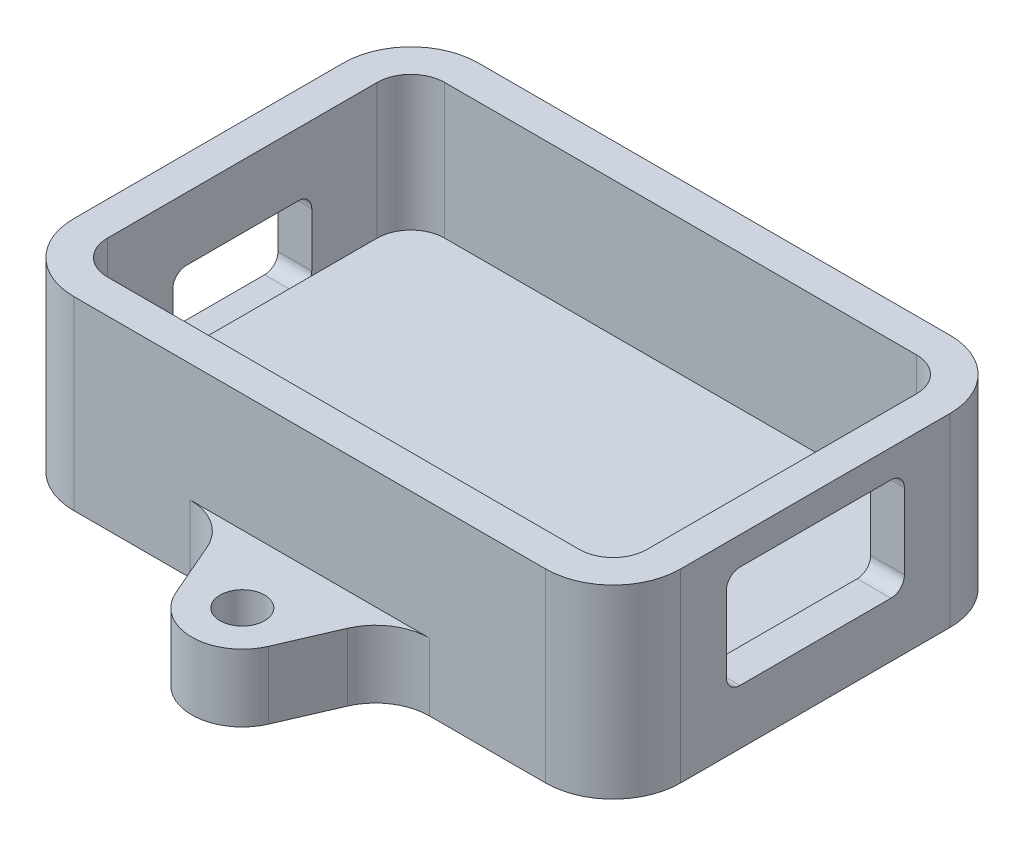
SolidWorks part; units mm, degrees
material "PVC Rigid"
ref_plane "Front Plane" through (0, 0, 0) normal (0, 0, 1) x (1, 0, 0)
ref_plane "Top Plane" through (0, 0, 0) normal (0, 1, 0) x (1, 0, 0)
ref_plane "Right Plane" through (0, 0, 0) normal (1, 0, 0) x (0, 0, -1)
sketch "Sketch1" plane through (0, 0, 0) normal (0, 1, 0) x (1, 0, 0)
  line L1 (-22.225, -19.05) -> (22.225, -19.05)
  line L2 (-28.575, -12.7) -> (-28.575, 12.7)
  line L3 (-22.225, 19.05) -> (22.225, 19.05)
  line L4 (28.575, -12.7) -> (28.575, 12.7)
  line L5 (-28.575, -19.05) -> (28.575, 19.05) construction
  line L6 (-28.575, 19.05) -> (28.575, -19.05) construction
  arc A0 (-22.225, -19.05) -> (-28.575, -12.7) centre (-22.225, -12.7) cw
  arc A1 (22.225, -19.05) -> (28.575, -12.7) centre (22.225, -12.7) ccw
  arc A2 (22.225, 19.05) -> (28.575, 12.7) centre (22.225, 12.7) cw
  arc A3 (-28.575, 12.7) -> (-22.225, 19.05) centre (-22.225, 12.7) cw
  point P0 (0, 0)
  dimension "D3" = 6.35
  dimension "D1" = 57.15
  dimension "D2" = 38.1
extrude "Boss-Extrude1" add sketch "Sketch1" along normal blind 4.7625
sketch "Sketch2" plane through (0, 4.7625, 0) normal (0, 1, 0) x (1, 0, 0)
  line L1 (-22.225, -15.875) -> (22.225, -15.875)
  line L2 (25.4, -12.7) -> (25.4, 12.7)
  line L3 (22.225, 15.875) -> (-22.225, 15.875)
  line L4 (-25.4, 12.7) -> (-25.4, -12.7)
  line L5 (-22.225, -19.05) -> (22.225, -19.05)
  line L6 (28.575, -12.7) -> (28.575, 12.7)
  line L7 (22.225, 19.05) -> (-22.225, 19.05)
  line L8 (-28.575, 12.7) -> (-28.575, -12.7)
  line L9 (-22.225, -19.05) -> (22.225, -19.05)
  line L10 (28.575, -12.7) -> (28.575, 12.7)
  line L11 (22.225, 19.05) -> (-22.225, 19.05)
  line L12 (-28.575, 12.7) -> (-28.575, -12.7)
  arc A0 (-25.4, -12.7) -> (-22.225, -15.875) centre (-22.225, -12.7) ccw
  arc A1 (22.225, -15.875) -> (25.4, -12.7) centre (22.225, -12.7) ccw
  arc A2 (25.4, 12.7) -> (22.225, 15.875) centre (22.225, 12.7) ccw
  arc A3 (-22.225, 15.875) -> (-25.4, 12.7) centre (-22.225, 12.7) ccw
  arc A4 (-28.575, -12.7) -> (-22.225, -19.05) centre (-22.225, -12.7) ccw
  arc A5 (22.225, -19.05) -> (28.575, -12.7) centre (22.225, -12.7) ccw
  arc A6 (28.575, 12.7) -> (22.225, 19.05) centre (22.225, 12.7) ccw
  arc A7 (-22.225, 19.05) -> (-28.575, 12.7) centre (-22.225, 12.7) ccw
  arc A8 (-28.575, -12.7) -> (-22.225, -19.05) centre (-22.225, -12.7) ccw
  arc A9 (22.225, -19.05) -> (28.575, -12.7) centre (22.225, -12.7) ccw
  arc A10 (28.575, 12.7) -> (22.225, 19.05) centre (22.225, 12.7) ccw
  arc A11 (-22.225, 19.05) -> (-28.575, 12.7) centre (-22.225, 12.7) ccw
  dimension "D1" = 0
  dimension "D2" = 3.175
extrude "Boss-Extrude2" add sketch "Sketch2" along normal blind 12.7
sketch "Sketch6" plane through (0, 0, 0) normal (0, -1, 0) x (1, 0, 0)
  line L0 (0, 0) -> (0, -25.4) construction
  line L1 (4.3707, -27.2916) -> (7.9375, -19.05)
  line L2 (22.225, -19.05) -> (-22.225, -19.05) construction
  line L3 (-4.3707, -27.2916) -> (-7.9375, -19.05)
  line L4 (7.9375, -19.05) -> (-7.9375, -19.05)
  circle A0 centre (0, -25.4) radius 2.1
  arc A1 (-4.3707, -27.2916) -> (4.3707, -27.2916) centre (0, -25.4) ccw
  dimension "D1" = 9.525
  dimension "D2" = 4.2
  dimension "D3" = 6.35
  dimension "D4" = 15.875
extrude "Boss-Extrude3" add sketch "Sketch6" against normal blind 6.35
sketch "Sketch4" plane through (-28.575, 0, 0) normal (-1, 0, 0) x (0, 0, 1)
  line L0 (-5.2705, 3.8989) -> (5.2705, 3.8989)
  line L1 (6.5405, 5.1689) -> (6.5405, 10.2489)
  line L2 (5.2705, 11.5189) -> (-5.2705, 11.5189)
  line L3 (-6.5405, 10.2489) -> (-6.5405, 5.1689)
  line L4 (-4.0005, 6.4389) -> (4.0005, 6.4389)
  line L5 (-4.0005, 8.9789) -> (-4.0005, 6.4389)
  line L6 (4.0005, 8.9789) -> (-4.0005, 8.9789)
  line L7 (4.0005, 6.4389) -> (4.0005, 8.9789)
  line L8 (-4.0005, 6.4389) -> (4.0005, 6.4389) construction
  line L9 (-4.0005, 8.9789) -> (-4.0005, 6.4389) construction
  line L10 (4.0005, 8.9789) -> (-4.0005, 8.9789) construction
  line L11 (4.0005, 6.4389) -> (4.0005, 8.9789) construction
  line L12 (-6.5405, 3.8989) -> (6.5405, 3.8989) construction
  line L13 (6.5405, 3.8989) -> (6.5405, 11.5189) construction
  line L14 (6.5405, 11.5189) -> (-6.5405, 11.5189) construction
  line L15 (-6.5405, 11.5189) -> (-6.5405, 3.8989) construction
  arc A0 (5.2705, 3.8989) -> (6.5405, 5.1689) centre (5.2705, 5.1689) ccw
  arc A1 (6.5405, 10.2489) -> (5.2705, 11.5189) centre (5.2705, 10.2489) ccw
  arc A2 (-5.2705, 3.8989) -> (-6.5405, 5.1689) centre (-5.2705, 5.1689) cw
  arc A3 (-5.2705, 11.5189) -> (-6.5405, 10.2489) centre (-5.2705, 10.2489) ccw
  dimension "D3" = 1.27
  dimension "D1" = 0
  dimension "D2" = 2.54
extrude "Cut-Extrude1" cut sketch "Sketch4" against normal up to surface (3.175 mm away) up to face at (-25.4, 11.1125, 0)
sketch "Sketch5" plane through (28.575, 0, 0) normal (1, 0, 0) x (0, 0, -1)
  line L0 (-7.112, 5.1689) -> (7.112, 5.1689)
  line L1 (8.382, 6.4389) -> (8.382, 13.5509)
  line L2 (7.112, 14.8209) -> (-7.112, 14.8209)
  line L3 (-8.382, 13.5509) -> (-8.382, 6.4389)
  line L4 (-7.112, 6.4389) -> (7.112, 6.4389)
  line L5 (-7.112, 13.5509) -> (-7.112, 6.4389)
  line L6 (7.112, 13.5509) -> (-7.112, 13.5509)
  line L7 (7.112, 6.4389) -> (7.112, 13.5509)
  line L8 (-7.112, 6.4389) -> (7.112, 6.4389) construction
  line L9 (-7.112, 13.5509) -> (-7.112, 6.4389) construction
  line L10 (7.112, 13.5509) -> (-7.112, 13.5509) construction
  line L11 (7.112, 6.4389) -> (7.112, 13.5509) construction
  line L12 (-8.382, 5.1689) -> (8.382, 5.1689) construction
  line L13 (-8.382, 14.8209) -> (-8.382, 5.1689) construction
  line L14 (8.382, 5.1689) -> (8.382, 14.8209) construction
  line L15 (8.382, 14.8209) -> (-8.382, 14.8209) construction
  arc A0 (-7.112, 5.1689) -> (-8.382, 6.4389) centre (-7.112, 6.4389) cw
  arc A1 (7.112, 5.1689) -> (8.382, 6.4389) centre (7.112, 6.4389) ccw
  arc A2 (8.382, 13.5509) -> (7.112, 14.8209) centre (7.112, 13.5509) ccw
  arc A3 (-7.112, 14.8209) -> (-8.382, 13.5509) centre (-7.112, 13.5509) ccw
  dimension "D3" = 1.27
  dimension "D1" = 0
  dimension "D2" = 1.27
extrude "Cut-Extrude2" cut sketch "Sketch5" against normal up to surface (3.175 mm away) up to face at (25.4, 11.1125, 0)
mirror "Mirror3" about plane through (0, 0, 0) normal (0, 0, 1) of "Boss-Extrude3"
fillet "Fillet1" radius 5.08 4 edges at (-7.9375, 3.175, -19.05) (-7.9375, 3.175, 19.05) (7.9375, 3.175, 19.05) (7.9375, 3.175, -19.05)
